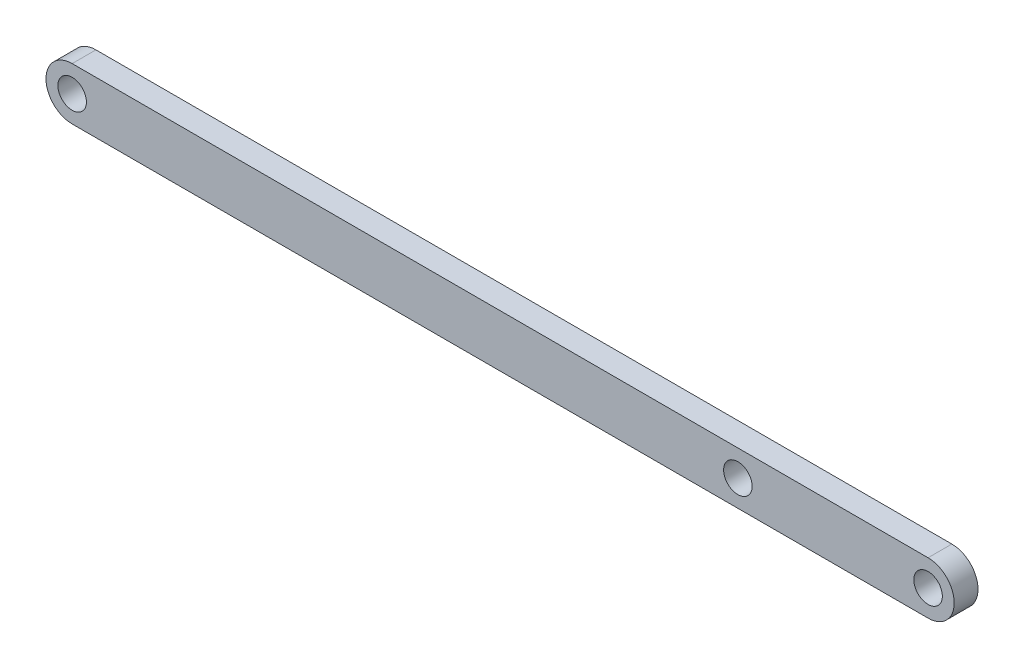
SolidWorks part; units mm, degrees
ref_plane "Front Plane" through (0, 0, 0) normal (0, 0, 1) x (1, 0, 0)
ref_plane "Top Plane" through (0, 0, 0) normal (0, 1, 0) x (1, 0, 0)
ref_plane "Right Plane" through (0, 0, 0) normal (1, 0, 0) x (0, 0, -1)
sketch "Sketch1" plane through (0, 0, 0) normal (0, 0, 1) x (1, 0, 0)
  line L0 (-90, 0) -> (90, 0) construction
  line L1 (-90, 5.5) -> (90, 5.5)
  line L2 (-90, -5.5) -> (90, -5.5)
  arc A0 (-90, 5.5) -> (-90, -5.5) centre (-90, 0) ccw
  arc A1 (90, -5.5) -> (90, 5.5) centre (90, 0) ccw
  circle A2 centre (-90, 0) radius 3
  circle A3 centre (90, 0) radius 3
  circle A4 centre (50, 0) radius 3
  point P2 (0, 0)
  dimension "D3" = 6
  dimension "D4" = 140
  dimension "D1" = 11
  dimension "D2" = 180
extrude "Boss-Extrude1" add sketch "Sketch1" along normal mid plane 5
